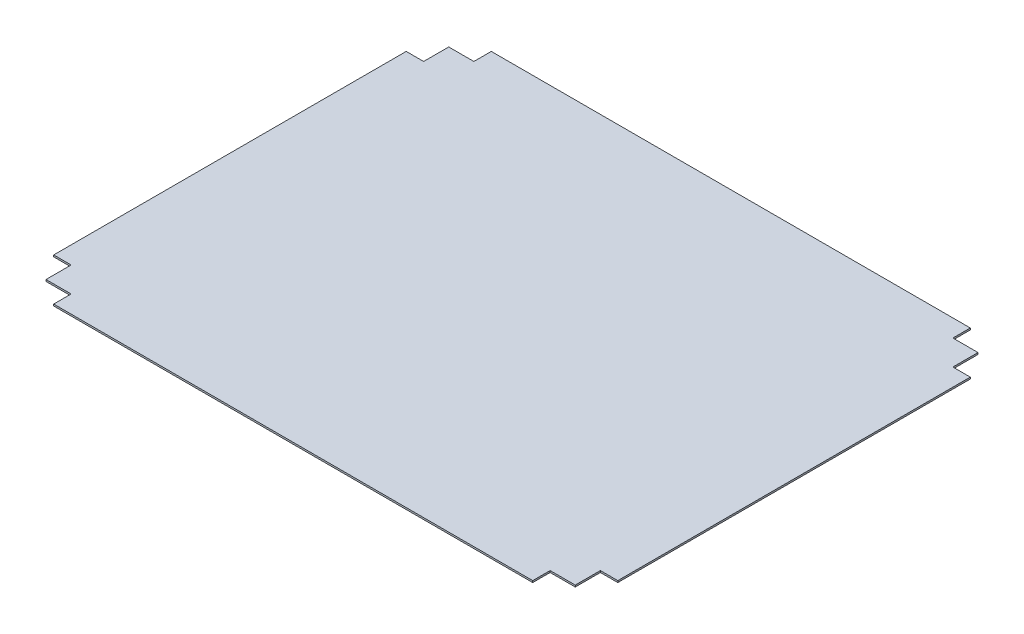
SolidWorks part; units mm, degrees
ref_plane "Front Plane" through (0, 0, 0) normal (0, 0, 1) x (1, 0, 0)
ref_plane "Top Plane" through (0, 0, 0) normal (0, 1, 0) x (1, 0, 0)
ref_plane "Right Plane" through (0, 0, 0) normal (1, 0, 0) x (0, 0, -1)
sketch "Sketch1" plane through (0, 0, 0) normal (0, 1, 0) x (1, 0, 0)
  line L0 (-276.3998, -252.5002) -> (-276.3998, -232.4011)
  line L1 (-276.3998, -232.4011) -> (-305.3998, -232.4011)
  line L2 (-305.3998, -232.4011) -> (-305.3998, -203.4011)
  line L3 (-305.3998, -203.4011) -> (-325.5002, -203.4011)
  line L4 (-325.5002, -203.4011) -> (-325.5002, 203.4011)
  line L5 (-325.5002, 203.4011) -> (-305.3998, 203.4011)
  line L6 (-305.3998, 203.4011) -> (-305.3998, 232.4011)
  line L7 (-305.3998, 232.4011) -> (-276.3998, 232.4011)
  line L8 (-276.3998, 232.4011) -> (-276.3998, 252.5002)
  line L9 (-276.3998, 252.5002) -> (276.4015, 252.5002)
  line L10 (276.4015, 252.5002) -> (276.4015, 232.4011)
  line L11 (276.4015, 232.4011) -> (305.4015, 232.4011)
  line L12 (305.4015, 232.4011) -> (305.4015, 203.4011)
  line L13 (305.4015, 203.4011) -> (325.5002, 203.4011)
  line L14 (325.5002, 203.4011) -> (325.5002, -203.4011)
  line L15 (325.5002, -203.4011) -> (305.4015, -203.4011)
  line L16 (305.4015, -203.4011) -> (305.4015, -232.4011)
  line L17 (305.4015, -232.4011) -> (276.4015, -232.4011)
  line L18 (276.4015, -232.4011) -> (276.4015, -252.5002)
  line L19 (276.4015, -252.5002) -> (-276.3998, -252.5002)
extrude "Boss-Extrude1" add sketch "Sketch1" along normal blind 2
